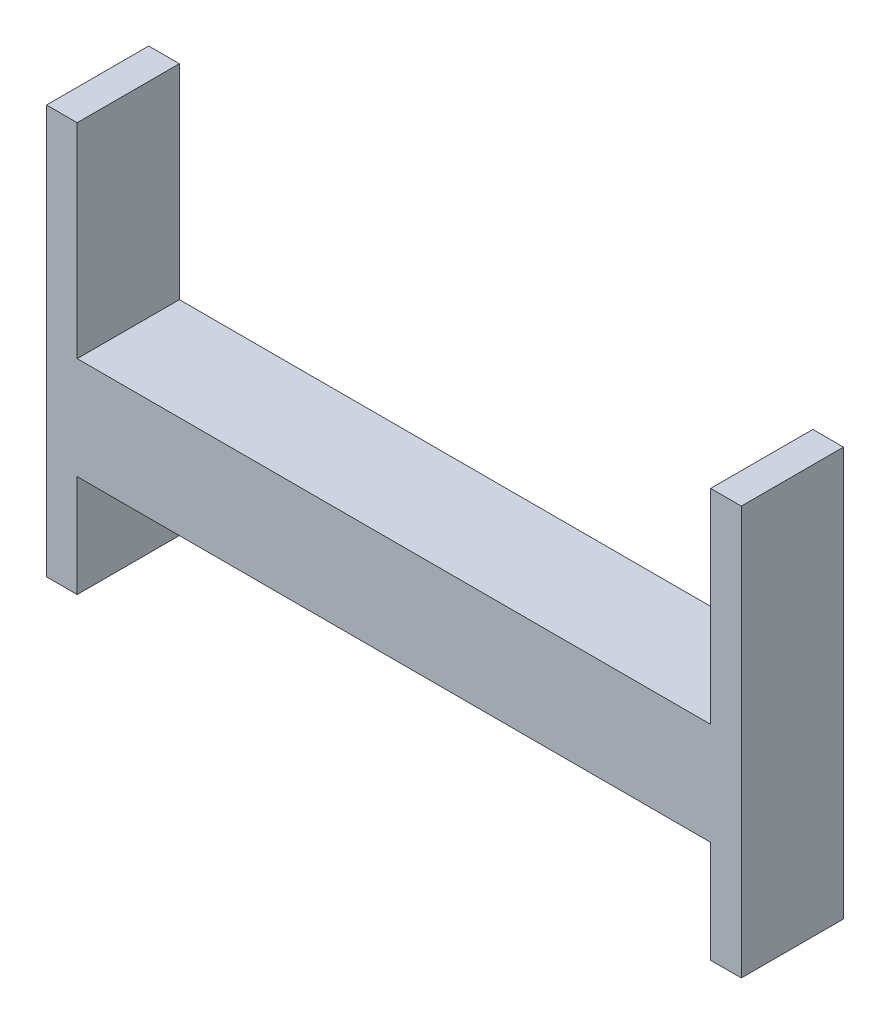
SolidWorks part; units mm, degrees
ref_plane "Alzado" through (0, 0, 0) normal (0, 0, 1) x (1, 0, 0)
ref_plane "Planta" through (0, 0, 0) normal (0, 1, 0) x (1, 0, 0)
ref_plane "Vista lateral" through (0, 0, 0) normal (1, 0, 0) x (0, 0, -1)
sketch "Croquis1" plane through (0, 0, 0) normal (0, 0, 1) x (1, 0, 0)
  line L0 (-170, -25) -> (-155, -25) construction
  line L5 (155, -25) -> (-155, -25)
  line L11 (155, 25) -> (-155, 25)
  line L14 (155, -25) -> (-155, 25) construction
  line L15 (155, 25) -> (-155, -25) construction
  line L21 (-155, 25) -> (-155, 125)
  line L22 (-155, 125) -> (-170, 125)
  line L23 (-170, -25) -> (-170, 125)
  line L25 (-170, -25) -> (-170, -75)
  line L26 (-170, -75) -> (-155, -75)
  line L27 (-155, -25) -> (-155, -75)
  line L28 (-155, 25) -> (-155, -25) construction
  line L29 (155, 25) -> (155, -25) construction
  line L30 (0, 75.5227) -> (0, -50.1198) construction
  line L31 (155, 125) -> (170, 125)
  line L32 (170, -75) -> (155, -75)
  line L33 (155, -25) -> (155, -75)
  line L34 (170, -25) -> (170, -75)
  line L35 (155, 25) -> (155, 125)
  line L36 (170, -25) -> (170, 125)
  point P0 (0, 0)
  dimension "D1" = 310
  dimension "D2" = 50
  dimension "D3" = 150
  dimension "D4" = 50
  dimension "D5" = 15
extrude "Saliente-Extruir3" add sketch "Croquis1" along normal blind 50
